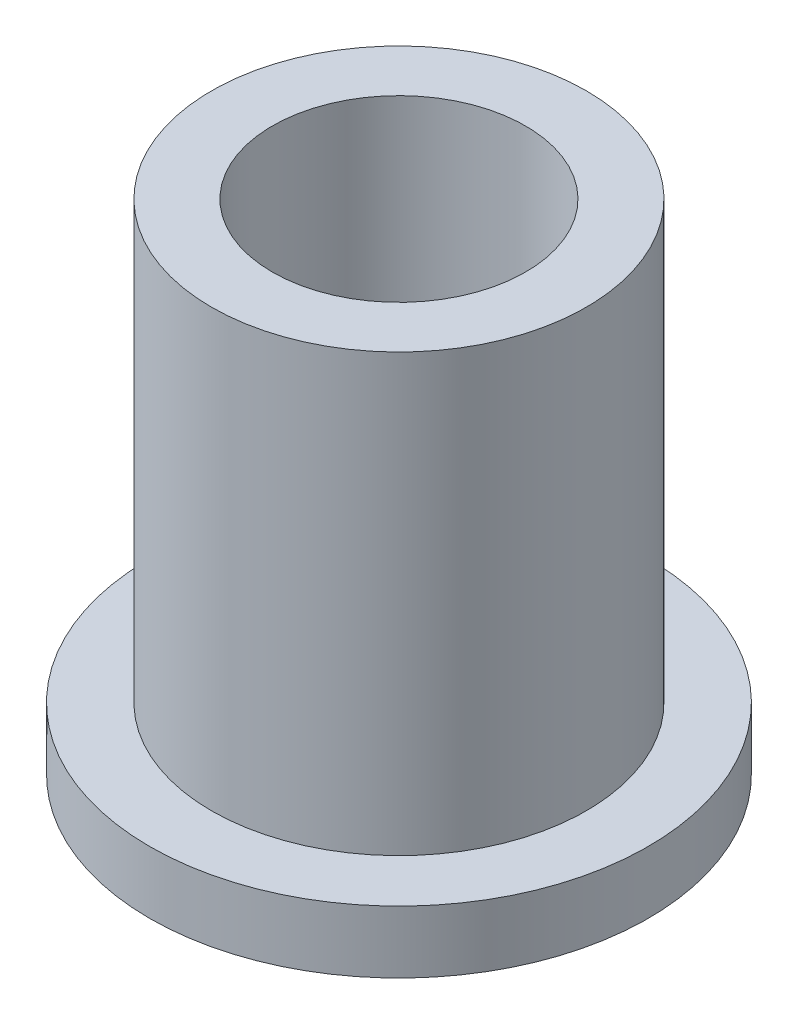
SolidWorks part; units mm, degrees
ref_plane "Front" through (0, 0, 0) normal (0, 0, 1) x (1, 0, 0)
ref_plane "Top" through (0, 0, 0) normal (0, 1, 0) x (1, 0, 0)
ref_plane "Right" through (0, 0, 0) normal (1, 0, 0) x (0, 0, -1)
sketch "Sketch1" plane through (0, 0, 0) normal (0, 1, 0) x (1, 0, 0)
  circle A0 centre (0, 0) radius 3.2258
  circle A1 centre (0, 0) radius 4.7752
  circle A2 centre (0, 0) radius 6.35
  dimension "ID" = 6.4516
  dimension "OD" = 9.5504
  dimension "FlangeOD" = 12.7
sketch "Sketch2" plane through (0, 0, 0) normal (0, 1, 0) x (1, 0, 0)
  circle A0 centre (0, 0) radius 3.2258 construction
  circle A1 centre (0, 0) radius 4.7752 construction
  circle A2 centre (0, 0) radius 3.2258
  circle A3 centre (0, 0) radius 4.7752
extrude "Boss-Extrude1" add sketch "Sketch2" along normal blind 12.7
sketch "Sketch3" plane through (0, 0, 0) normal (0, 1, 0) x (1, 0, 0)
  circle A0 centre (0, 0) radius 6.35 construction
  circle A1 centre (0, 0) radius 4.7752 construction
  circle A2 centre (0, 0) radius 6.35
  circle A3 centre (0, 0) radius 4.7752
extrude "Boss-Extrude2" add sketch "Sketch3" along normal blind 1.5875
